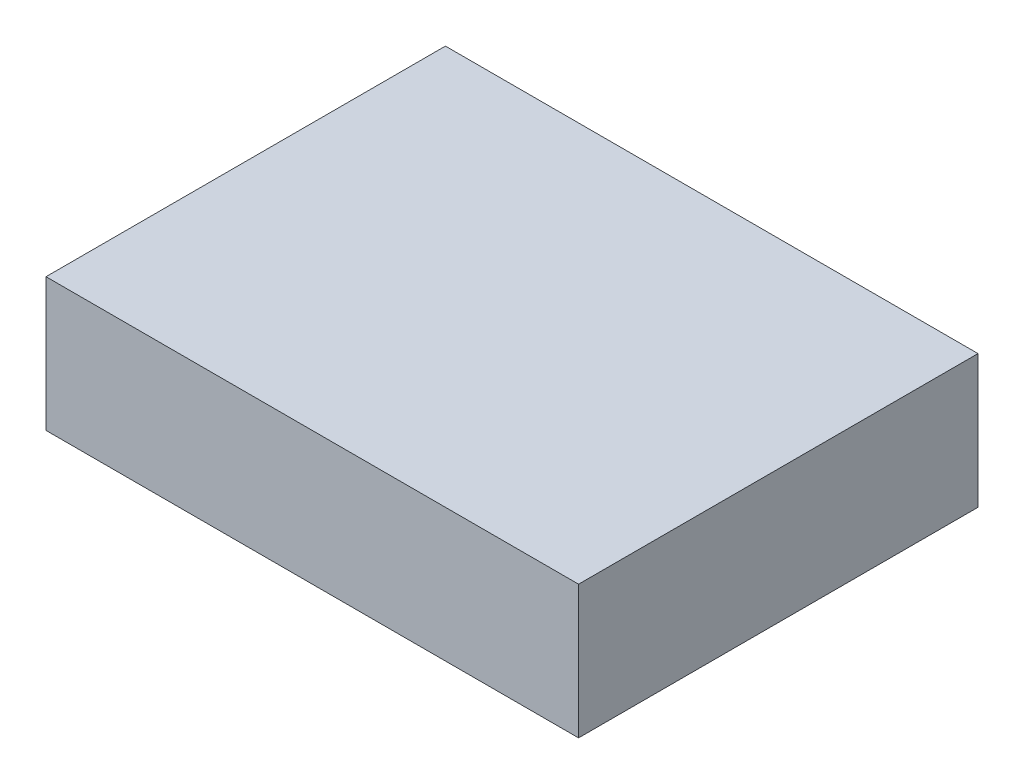
SolidWorks part; units mm, degrees
ref_plane "Front Plane" through (0, 0, 0) normal (0, 0, 1) x (1, 0, 0)
ref_plane "Top Plane" through (0, 0, 0) normal (0, 1, 0) x (1, 0, 0)
ref_plane "Right Plane" through (0, 0, 0) normal (1, 0, 0) x (0, 0, -1)
sketch "Sketch1" plane through (0, 0, 0) normal (0, 1, 0) x (1, 0, 0)
  line L1 (-150.4717, 151.4151) -> (249.5283, 151.4151)
  line L2 (-150.4717, 151.4151) -> (-150.4717, -148.5849)
  line L3 (-150.4717, -148.5849) -> (249.5283, -148.5849)
  line L4 (249.5283, 151.4151) -> (249.5283, -148.5849)
  dimension "D1" = 300
  dimension "D2" = 400
extrude "Boss-Extrude1" add sketch "Sketch1" along normal blind 100
